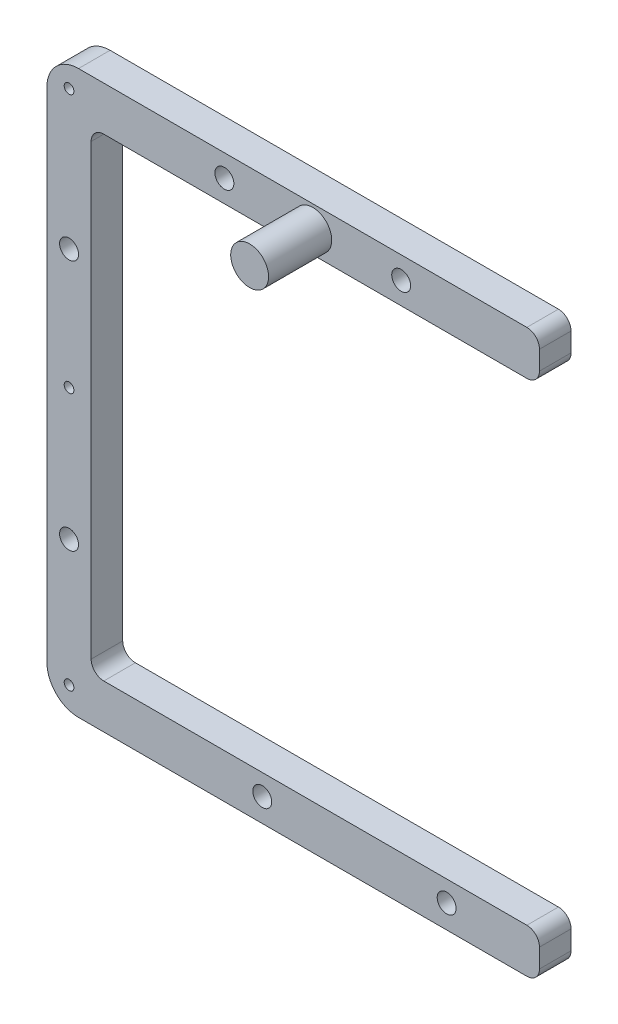
SolidWorks part; units mm, degrees
ref_plane "Front Plane" through (0, 0, 0) normal (0, 0, 1) x (1, 0, 0)
ref_plane "Top Plane" through (0, 0, 0) normal (0, 1, 0) x (1, 0, 0)
ref_plane "Right Plane" through (0, 0, 0) normal (1, 0, 0) x (0, 0, -1)
sketch "Sketch1" plane through (0, 0, 0) normal (0, 0, 1) x (1, 0, 0)
  line L8 (0, 35.5) -> (0, -35.5)
  line L9 (2, 37.5) -> (69, 37.5)
  line L10 (2, -37.5) -> (69, -37.5)
  line L11 (-2, 44.5) -> (69, 44.5)
  line L12 (-7, 39.5) -> (-7, -39.5)
  line L13 (-2, -44.5) -> (69, -44.5)
  line L14 (71, 42.5) -> (71, 39.5)
  line L15 (71, -39.5) -> (71, -42.5)
  line L16 (-7, 44.5) -> (-7, -44.5) construction
  line L17 (-7, -44.5) -> (71, -44.5) construction
  line L18 (-7, 44.5) -> (71, 44.5) construction
  line L19 (0, 37.5) -> (0, -37.5) construction
  line L20 (0, 37.5) -> (71, 37.5) construction
  line L21 (0, -37.5) -> (71, -37.5) construction
  arc A4 (-7, -39.5) -> (-2, -44.5) centre (-2, -39.5) ccw
  arc A5 (-2, 44.5) -> (-7, 39.5) centre (-2, 39.5) ccw
  arc A6 (0, 35.5) -> (2, 37.5) centre (2, 35.5) cw
  arc A7 (0, -35.5) -> (2, -37.5) centre (2, -35.5) ccw
  arc A8 (69, -44.5) -> (71, -42.5) centre (69, -42.5) ccw
  arc A9 (69, -37.5) -> (71, -39.5) centre (69, -39.5) cw
  arc A10 (69, 37.5) -> (71, 39.5) centre (69, 39.5) ccw
  arc A11 (69, 44.5) -> (71, 42.5) centre (69, 42.5) cw
  point P3 (0, 0)
  point P19 (0, 37.5)
  dimension "D4" = 5
  dimension "D5" = 2
  dimension "D3" = 7
extrude "Boss-Extrude1" add sketch "Sketch1" along normal blind 5
sketch "Sketch2" plane through (0, 0, 5) normal (0, 0, 1) x (1, 0, 0)
  line L0 (71, -41) -> (1.5407, -41) construction
  line L1 (71, -42.5) -> (71, -39.5) construction
  line L2 (0, -35.5) -> (0, 35.5) construction
  line L3 (35.1, -41) -> (35.1, 47.4599) construction
  line L4 (71, 41) -> (-16.6405, 41) construction
  line L5 (71, 39.5) -> (71, 42.5) construction
  circle A1 centre (35.1, 41) radius 3
  dimension "D2" = 35.1
extrude "Boss-Extrude2" add sketch "Sketch2" along normal blind 10
sketch "Sketch3" plane through (0, 0, 5) normal (0, 0, 1) x (1, 0, 0)
  line L0 (35.1, 41) -> (35.1, 14.4779) construction
  line L1 (35.1, 41) -> (84.8794, 41) construction
  line L2 (35.1, 41) -> (-23.3237, 41) construction
  line L3 (-3.5, 49.9091) -> (-3.5, -39.0819) construction
  line L4 (-7, 39.5) -> (-7, -39.5) construction
  line L5 (-11.872, -40.8) -> (89.7097, -40.8) construction
  circle A0 centre (49.1, 41) radius 1.5
  circle A1 centre (21.1, 41) radius 1.5
  circle A2 centre (-3.5, 19) radius 1.5
  circle A3 centre (-3.5, -20.8) radius 1.5
  circle A4 centre (27.1, -40.8) radius 1.5
  circle A5 centre (56.3, -40.8) radius 1.5
  dimension "D1" = 3
  dimension "D2" = 3
  dimension "D7" = 3
  dimension "D8" = 3
  dimension "D11" = 3
  dimension "D13" = 3
  dimension "D3" = 14
  dimension "D4" = 14
  dimension "D5" = 3.5
  dimension "D6" = 22
  dimension "D9" = 39.8
  dimension "D10" = 20
  dimension "D12" = 8
  dimension "D14" = 29.2
extrude "Cut-Extrude1" cut sketch "Sketch3" against normal through all
sketch "Sketch4" plane through (0, 0, 5) normal (0, 0, 1) x (1, 0, 0)
  line L0 (35.1, 41) -> (-13.9251, 41) construction
  line L1 (27.1, -40.8) -> (-15.696, -40.8) construction
  line L2 (-3.5, 19) -> (-3.5, -46.0432) construction
  line L3 (-3.5, 19) -> (-3.5, 47.696) construction
  line L4 (-3.5, -20.8) -> (3.0991, -20.8) construction
  circle A0 centre (-3.5, 0) radius 0.77
  circle A1 centre (-3.5, 41) radius 0.77
  circle A2 centre (-3.5, -40.8) radius 0.77
  point P15 (0, 0)
  point P16 (-13.9251, -1.2056)
  point P22 (0, 0)
  point P23 (-10.3922, -8.5498)
  point P24 (0, 0)
  dimension "D1" = 1.54
extrude "Cut-Extrude2" cut sketch "Sketch4" against normal blind 3
cosmetic thread "Cosmetic Thread1" parameters "D2"=2
cosmetic thread "Cosmetic Thread2" parameters "D2"=2
cosmetic thread "Cosmetic Thread3" parameters "D2"=2
